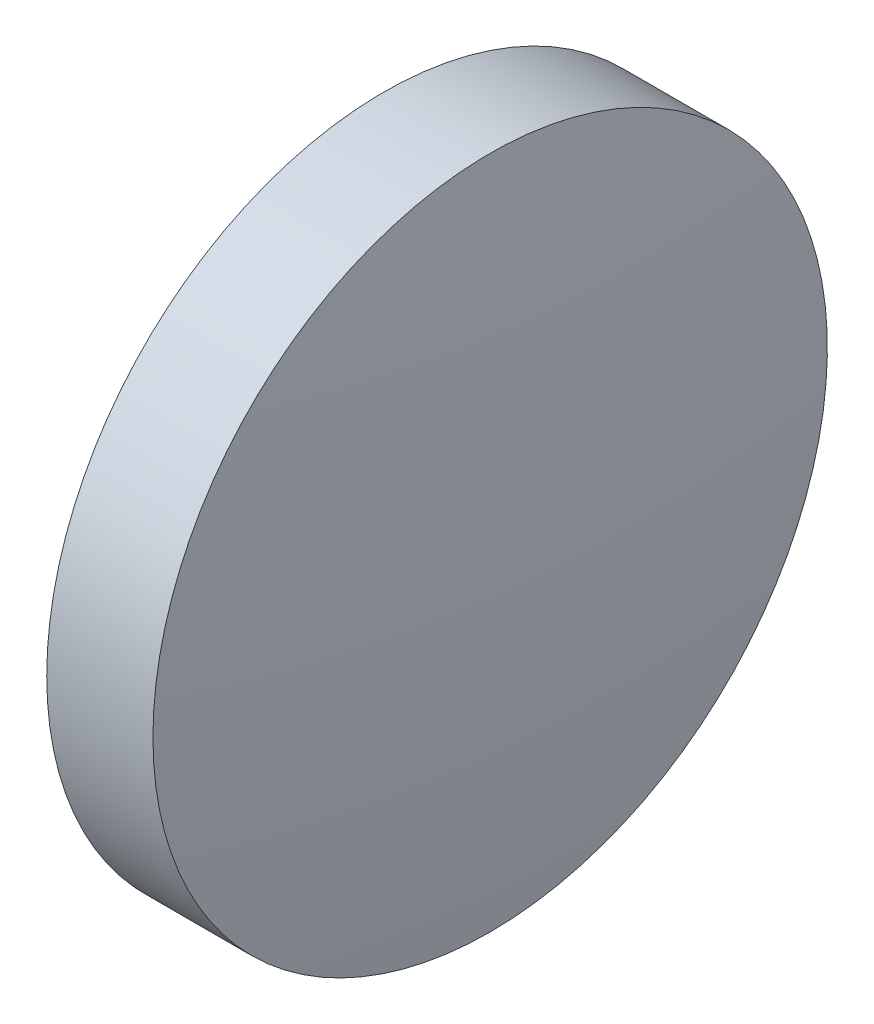
SolidWorks part; units mm, degrees
ref_plane "前视基准面" through (0, 0, 0) normal (0, 0, 1) x (1, 0, 0)
ref_plane "上视基准面" through (0, 0, 0) normal (0, 1, 0) x (1, 0, 0)
ref_plane "右视基准面" through (0, 0, 0) normal (1, 0, 0) x (0, 0, -1)
sketch "草图1" plane through (0, 0, 0) normal (0, 0, 1) x (1, 0, 0)
  line L0 (457.5007, 237.4846) -> (465.0191, 237.4846) construction
  line L1 (459.7612, 237.4846) -> (459.7612, 243.8346)
  line L2 (462.1612, 237.4846) -> (459.7612, 237.4846)
  line L5 (459.7612, 243.8346) -> (461.7612, 243.8346)
  arc A0 (462.1612, 237.4846) -> (461.7612, 243.8346) centre (411.5581, 237.4846) ccw
revolve "旋转1" add sketch "草图1" angle 360 about L0
